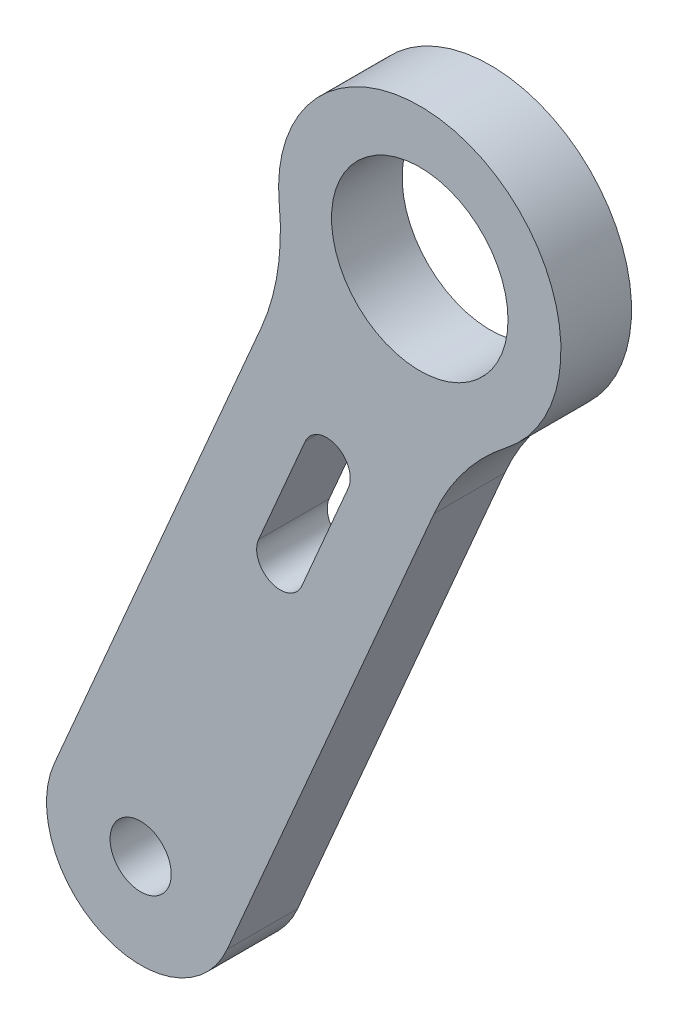
SolidWorks part; units mm, degrees
ref_plane "Front Plane" through (0, 0, 0) normal (0, 0, 1) x (1, 0, 0)
ref_plane "Top Plane" through (0, 0, 0) normal (0, 1, 0) x (1, 0, 0)
ref_plane "Right Plane" through (0, 0, 0) normal (1, 0, 0) x (0, 0, -1)
sketch "Model" plane through (0, 0, 0) normal (0, 0, 1) x (1, 0, 0)
  line L0 (59.6479, 46.4567) -> (50.849, 26.0161)
  line L1 (63.3493, 42.4095) -> (61.3724, 37.8169)
  line L2 (61.5123, 43.2003) -> (59.5354, 38.6077)
  line L3 (58.1972, 22.853) -> (66.9961, 43.2937)
  circle A0 centre (54.5231, 24.4346) radius 1.3
  arc A1 (50.849, 26.0161) -> (58.1972, 22.853) centre (54.5231, 24.4346) ccw
  arc A2 (59.6479, 46.4567) -> (60.4139, 51.3977) centre (50.463, 50.4105) ccw
  arc A3 (70.0583, 47.2461) -> (66.9961, 43.2937) centre (76.181, 39.3399) ccw
  arc A4 (70.0583, 47.2461) -> (60.4139, 51.3977) centre (66.3846, 51.99) ccw
  circle A5 centre (66.3847, 51.99) radius 3.75
  arc A6 (59.5354, 38.6077) -> (61.3724, 37.8169) centre (60.4539, 38.2123) ccw
  arc A7 (63.3493, 42.4095) -> (61.5123, 43.2003) centre (62.4308, 42.8049) ccw
extrude "Boss-Extrude1" add sketch "Model" along normal blind 3
